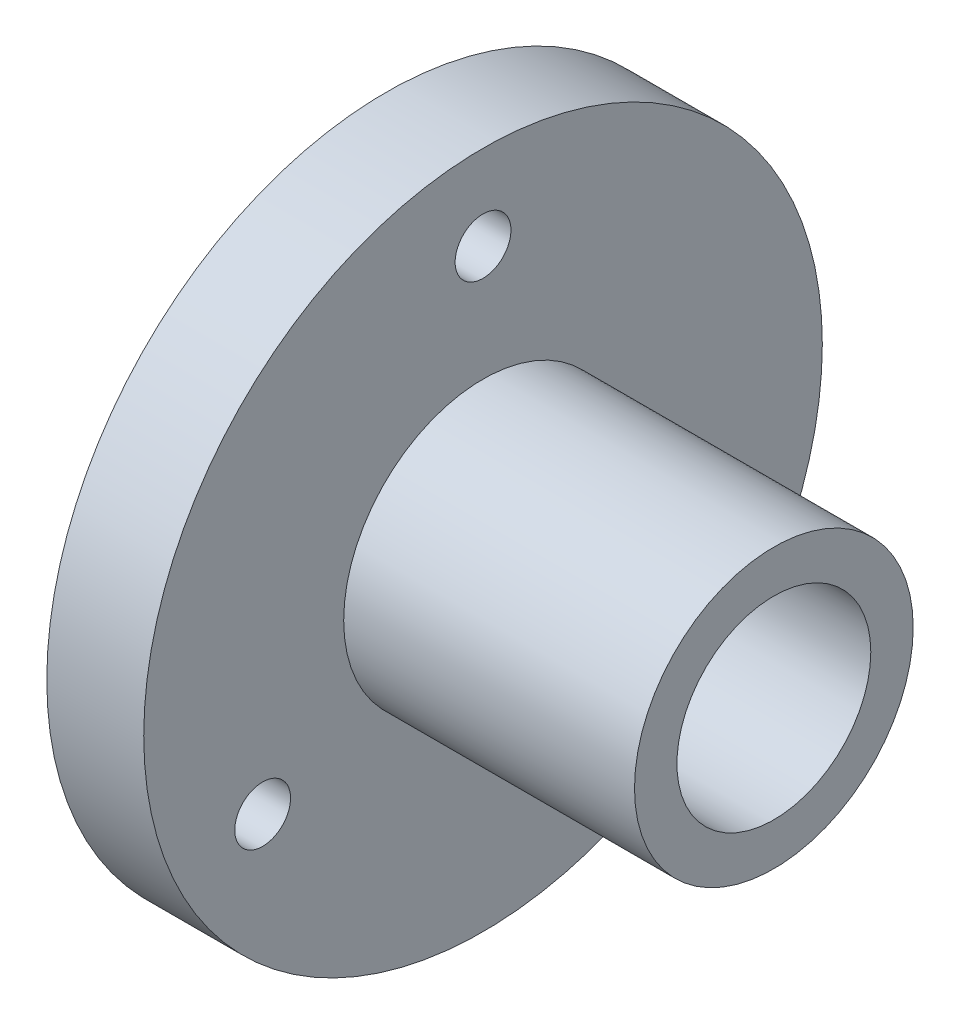
SolidWorks part; units mm, degrees
ref_plane "正面" through (0, 0, 0) normal (0, 0, 1) x (1, 0, 0)
ref_plane "平面" through (0, 0, 0) normal (0, 1, 0) x (1, 0, 0)
ref_plane "右側面" through (0, 0, 0) normal (1, 0, 0) x (0, 0, -1)
sketch "ｽｹｯﾁ1" plane through (0, 0, 0) normal (1, 0, 0) x (0, 0, -1)
  line L0 (0, 55) -> (0, -55) construction
  circle A0 centre (0, 0) radius 14
  circle A1 centre (0, 10.5) radius 1.1514
  circle A2 centre (9.0933, -5.25) radius 1.1514
  circle A3 centre (-9.0933, -5.25) radius 1.1514
  point P14 (0, 0)
  dimension "D1" = 28
  dimension "D2" = 3
extrude "ﾎﾞｽ - 押し出し1" add sketch "ｽｹｯﾁ1" along normal blind 4
sketch "ｽｹｯﾁ2" plane through (4, 0, 0) normal (1, 0, 0) x (0, 0, -1)
  circle A0 centre (0, 0) radius 5.75
  dimension "D1" = 11.5
extrude "ﾎﾞｽ - 押し出し2" add sketch "ｽｹｯﾁ2" along normal blind 12
sketch "ｽｹｯﾁ3" plane through (16, 0, 0) normal (1, 0, 0) x (0, 0, -1)
  circle A0 centre (0, 0) radius 4
  dimension "D1" = 8
extrude "ｶｯﾄ - 押し出し1" cut sketch "ｽｹｯﾁ3" against normal blind 16 contours A0
